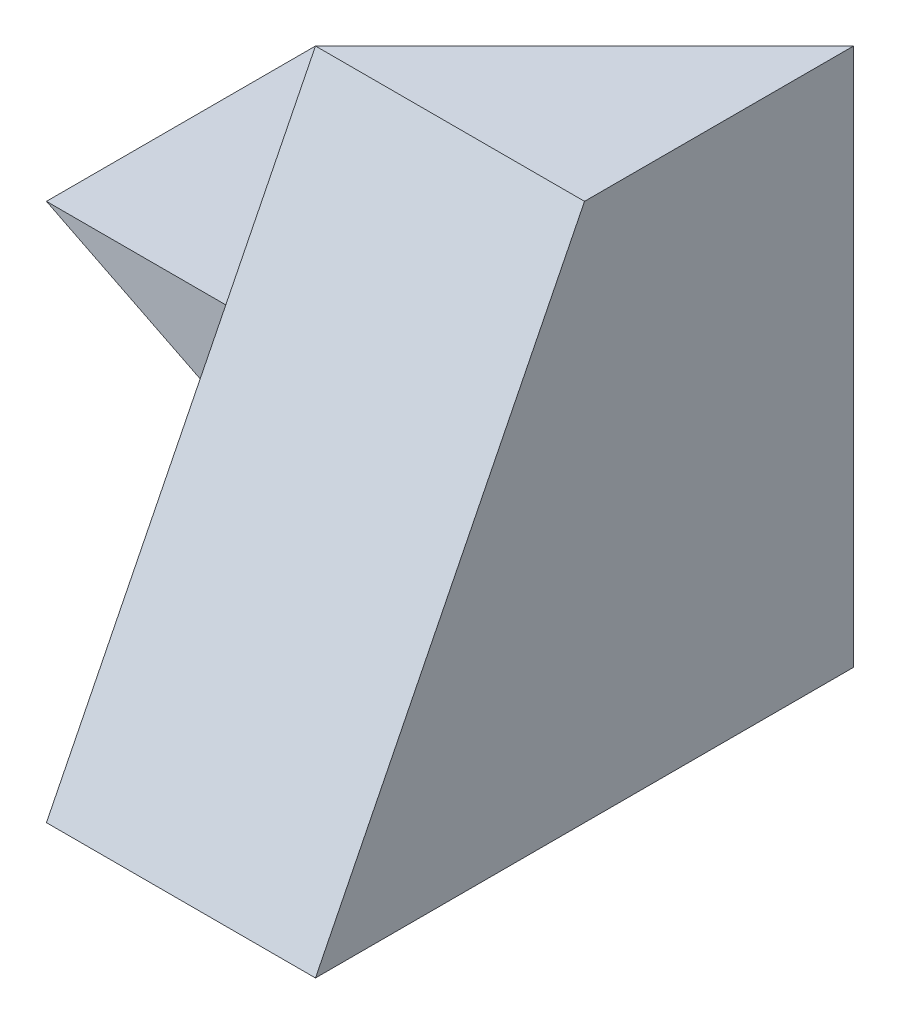
SolidWorks part; units mm, degrees
ref_plane "Front Plane" through (0, 0, 0) normal (0, 0, 1) x (1, 0, 0)
ref_plane "Top Plane" through (0, 0, 0) normal (0, 1, 0) x (1, 0, 0)
ref_plane "Right Plane" through (0, 0, 0) normal (1, 0, 0) x (0, 0, -1)
sketch "Sketch1" plane through (0, 0, 0) normal (0, 0, 1) x (1, 0, 0)
  line L1 (0, 0) -> (40, 0)
  line L2 (0, 0) -> (0, 40)
  line L3 (0, 40) -> (40, 40)
  line L4 (40, 0) -> (40, 40)
  dimension "D1" = 40
  dimension "D2" = 40
extrude "Boss-Extrude1" add sketch "Sketch1" along normal blind 40
sketch "Sketch2" plane through (0, 0, 40) normal (0, 0, 1) x (1, 0, 0)
  line L1 (0, 40) -> (20, 40)
  line L2 (0, 40) -> (0, 20)
  line L3 (0, 20) -> (20, 20)
  line L4 (20, 40) -> (20, 20)
  dimension "D1" = 20
  dimension "D2" = 20
extrude "Cut-Extrude1" cut sketch "Sketch2" against normal blind 40
sketch "Sketch3" plane through (0, 0, 40) normal (0, 0, 1) x (1, 0, 0)
  line L0 (0, 0) -> (20, 0)
  line L1 (0, 0) -> (40, 0) construction
  line L2 (20, 0) -> (20, 10)
  line L3 (20, 10) -> (0, 20)
  line L4 (0, 20) -> (0, 0)
  dimension "D1" = 10
extrude "Cut-Extrude2" cut sketch "Sketch3" against normal blind 40
sketch "Sketch4" plane through (40, 0, 0) normal (1, 0, 0) x (0, 0, -1)
  line L0 (-40, 0) -> (-20, 40)
  line L1 (-40, 40) -> (0, 40) construction
  line L2 (-20, 40) -> (-40, 40)
  line L3 (-40, 40) -> (-40, 0)
extrude "Cut-Extrude3" cut sketch "Sketch4" against normal blind 40
sketch "Sketch5" plane through (0, 0, 0) normal (0, -1, 0) x (1, 0, 0)
  line L1 (20, 40) -> (0, 40)
  line L2 (20, 40) -> (20, 20)
  line L3 (20, 20) -> (0, 20)
  line L4 (0, 40) -> (0, 20)
  dimension "D1" = 20
  dimension "D2" = 20
extrude "Cut-Extrude4" cut sketch "Sketch5" against normal blind 40
sketch "Sketch6" plane through (0, 0, 0) normal (0, 0, -1) x (-1, 0, 0)
  line L0 (-20, 10) -> (-40, 0)
  line L1 (-40, 0) -> (-20, 0)
  line L2 (-20, 0) -> (-20, 10)
  line L3 (-20, 10) -> (-40, 0)
  line M6 (-40, 0) -> (-20, 0)
  line M7 (-20, 0) -> (-20, 10)
extrude "Cut-Extrude5" cut sketch "Sketch6" against normal blind 20 contours L0 M7 M6
sketch "Sketch9" plane through (0, 40, 0) normal (0, 1, 0) x (1, 0, 0)
  line L0 (20, -20) -> (40, 0)
  line L1 (40, 0) -> (20, 0)
  line L2 (20, 0) -> (20, -20)
extrude "Cut-Extrude13" cut sketch "Sketch9" against normal blind 20
